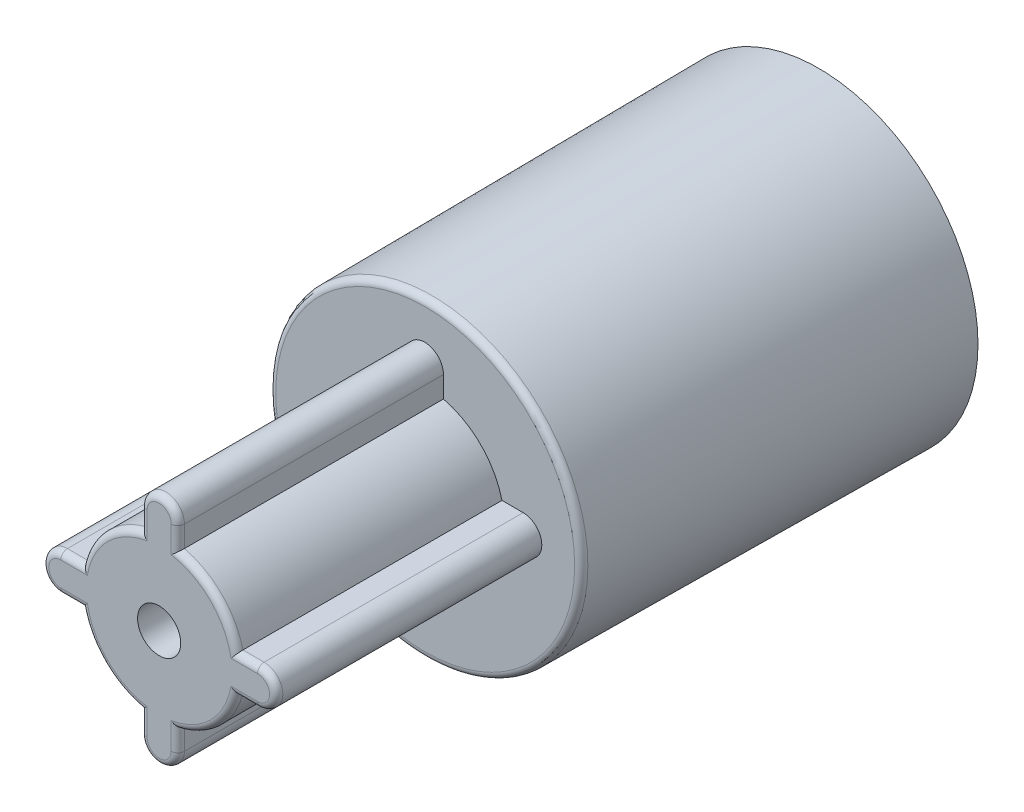
SolidWorks part; units mm, degrees
ref_plane "Plane1" through (0, 0, 0) normal (0, 0, 1) x (1, 0, 0)
ref_plane "Plane2" through (0, 0, 0) normal (0, 1, 0) x (1, 0, 0)
ref_plane "Plane3" through (0, 0, 0) normal (1, 0, 0) x (0, 0, -1)
other "Configuration Table"
sketch "Sketch1" plane through (0, 0, 0) normal (0, 0, 1) x (1, 0, 0)
  circle A0 centre (0, 0) radius 9.6
  dimension "D1" = 19.2
extrude "Base-Extrude" add sketch "Sketch1" along normal blind 23.7
sketch "Sketch2" plane through (0, 0, 0) normal (0, 0, -1) x (-1, 0, 0)
  line L0 (1.1513, 6.0166) -> (1.1513, 4.7416)
  line L1 (5.9522, 1.2157) -> (4.6772, 1.2157)
  line L2 (-5.8995, 1.2157) -> (-4.6245, 1.2157)
  line L3 (-1.0987, 6.0166) -> (-1.0987, 4.7416)
  line L4 (-5.8995, -1.0343) -> (-4.6245, -1.0343)
  line L5 (1.1513, -5.8351) -> (1.1513, -4.5601)
  line L6 (5.9522, -1.0343) -> (4.6772, -1.0343)
  line L7 (-1.0987, -4.5601) -> (-1.0987, -5.8351)
  arc A0 (4.6772, 1.2157) -> (1.1513, 4.7416) centre (0.0263, 0.0907) ccw
  arc A1 (5.9522, -1.0343) -> (7.0772, 0.0907) centre (5.9522, 0.0907) ccw
  arc A2 (7.0772, 0.0907) -> (5.9522, 1.2157) centre (5.9522, 0.0907) ccw
  arc A3 (-5.8995, 1.2157) -> (-7.0245, 0.0907) centre (-5.8995, 0.0907) ccw
  arc A4 (-1.0987, 4.7416) -> (-4.6245, 1.2157) centre (0.0263, 0.0907) ccw
  arc A5 (0.0263, 7.1416) -> (-1.0987, 6.0166) centre (0.0263, 6.0166) ccw
  arc A6 (1.1513, 6.0166) -> (0.0263, 7.1416) centre (0.0263, 6.0166) ccw
  arc A7 (-7.0245, 0.0907) -> (-5.8995, -1.0343) centre (-5.8995, 0.0907) ccw
  arc A8 (-4.6245, -1.0343) -> (-1.0987, -4.5601) centre (0.0263, 0.0907) ccw
  arc A9 (-1.0987, -5.8351) -> (1.1513, -5.8351) centre (0.0263, -5.8351) ccw
  arc A10 (1.1513, -4.5601) -> (4.6772, -1.0343) centre (0.0263, 0.0907) ccw
extrude "Cut-Extrude1" cut sketch "Sketch2" against normal blind 21.7
sketch "Sketch3" plane through (0, 0, 23.7) normal (0, 0, 1) x (1, 0, 0)
  line L8 (-1.1513, 6.0166) -> (-1.1513, 4.7416)
  line L9 (-5.9522, 1.2157) -> (-4.6772, 1.2157)
  line L10 (-5.9522, -1.0343) -> (-4.6772, -1.0343)
  line L11 (-1.1513, -5.8351) -> (-1.1513, -4.5601)
  line L12 (1.0987, -4.5601) -> (1.0987, -5.8351)
  line L13 (5.8995, -1.0343) -> (4.6245, -1.0343)
  line L14 (5.8995, 1.2157) -> (4.6245, 1.2157)
  line L15 (1.0987, 6.0166) -> (1.0987, 4.7416)
  line L16 (-1.1513, 6.0166) -> (-1.1513, 4.7416)
  line L17 (-5.9522, 1.2157) -> (-4.6772, 1.2157)
  line L18 (-5.9522, -1.0343) -> (-4.6772, -1.0343)
  line L19 (-1.1513, -5.8351) -> (-1.1513, -4.5601)
  line L20 (1.0987, -4.5601) -> (1.0987, -5.8351)
  line L21 (5.8995, -1.0343) -> (4.6245, -1.0343)
  line L22 (5.8995, 1.2157) -> (4.6245, 1.2157)
  line L23 (1.0987, 6.0166) -> (1.0987, 4.7416)
  arc A11 (-1.1513, 4.7416) -> (-4.6772, 1.2157) centre (-0.0263, 0.0907) ccw
  arc A12 (-5.9522, 1.2157) -> (-7.0772, 0.0907) centre (-5.9522, 0.0907) ccw
  arc A13 (-7.0772, 0.0907) -> (-5.9522, -1.0343) centre (-5.9522, 0.0907) ccw
  arc A14 (-4.6772, -1.0343) -> (-1.1513, -4.5601) centre (-0.0263, 0.0907) ccw
  arc A15 (-1.1513, -5.8351) -> (1.0987, -5.8351) centre (-0.0263, -5.8351) ccw
  arc A16 (1.0987, -4.5601) -> (4.6245, -1.0343) centre (-0.0263, 0.0907) ccw
  arc A17 (5.8995, -1.0343) -> (7.0245, 0.0907) centre (5.8995, 0.0907) ccw
  arc A18 (7.0245, 0.0907) -> (5.8995, 1.2157) centre (5.8995, 0.0907) ccw
  arc A19 (4.6245, 1.2157) -> (1.0987, 4.7416) centre (-0.0263, 0.0907) ccw
  arc A20 (1.0987, 6.0166) -> (-0.0263, 7.1416) centre (-0.0263, 6.0166) ccw
  arc A21 (-0.0263, 7.1416) -> (-1.1513, 6.0166) centre (-0.0263, 6.0166) ccw
  arc A22 (-1.1513, 4.7416) -> (-4.6772, 1.2157) centre (-0.0263, 0.0907) ccw
  arc A23 (-5.9522, 1.2157) -> (-7.0772, 0.0907) centre (-5.9522, 0.0907) ccw
  arc A24 (-7.0772, 0.0907) -> (-5.9522, -1.0343) centre (-5.9522, 0.0907) ccw
  arc A25 (-4.6772, -1.0343) -> (-1.1513, -4.5601) centre (-0.0263, 0.0907) ccw
  arc A26 (-1.1513, -5.8351) -> (1.0987, -5.8351) centre (-0.0263, -5.8351) ccw
  arc A27 (1.0987, -4.5601) -> (4.6245, -1.0343) centre (-0.0263, 0.0907) ccw
  arc A28 (5.8995, -1.0343) -> (7.0245, 0.0907) centre (5.8995, 0.0907) ccw
  arc A29 (7.0245, 0.0907) -> (5.8995, 1.2157) centre (5.8995, 0.0907) ccw
  arc A30 (4.6245, 1.2157) -> (1.0987, 4.7416) centre (-0.0263, 0.0907) ccw
  arc A31 (1.0987, 6.0166) -> (-0.0263, 7.1416) centre (-0.0263, 6.0166) ccw
  arc A32 (-0.0263, 7.1416) -> (-1.1513, 6.0166) centre (-0.0263, 6.0166) ccw
  dimension "D1" = 0
extrude "Boss-Extrude1" add sketch "Sketch3" along normal blind 16
sketch "Sketch4" plane through (0, 0, 39.7) normal (0, 0, 1) x (1, 0, 0)
  circle A0 centre (-0.0263, 0.0907) radius 1.3
  dimension "D1" = 2.6
extrude "Cut-Extrude2" cut sketch "Sketch4" against normal through all
sketch "Sketch5" plane through (0, 0, 0) normal (1, 0, 0) x (0, 0, -1)
  line L0 (0, 0) -> (-41.9103, 0) construction
  line L1 (-23.7, 0) -> (0, 0) construction
  line L3 (0, 9.6) -> (-23.7, 9.4)
  line L4 (0, -9.6) -> (0, 9.6) construction
  line L6 (-23.7, 9.6) -> (-23.7, -9.6) construction
  line L7 (-23.7, 9.4) -> (-23.7, 9.6)
  line L10 (-23.7, 9.6) -> (0, 9.6)
  dimension "D1" = 0.2
revolve "Cut-Revolve1" cut sketch "Sketch5" angle 360 about L0
fillet "Fillet4" radius 0.4 17 edges at (-9.4, 0, 23.7) (-5.3147, 1.2157, 39.7) (-1.1513, -5.1976, 39.7) (1.0987, -5.1976, 39.7) (5.262, -1.0343, 39.7) (1.0987, 5.3791, 39.7) (-0.0263, 7.1416, 39.7) (-1.1513, 5.3791, 39.7) (-3.4098, 3.4742, 39.7) (-7.0772, 0.0907, 39.7) (-5.3147, -1.0343, 39.7) (-3.4098, -3.2928, 39.7) (-0.0263, -6.9601, 39.7) (3.3572, -3.2928, 39.7) (7.0245, 0.0907, 39.7) (5.262, 1.2157, 39.7) (3.3572, 3.4742, 39.7)
